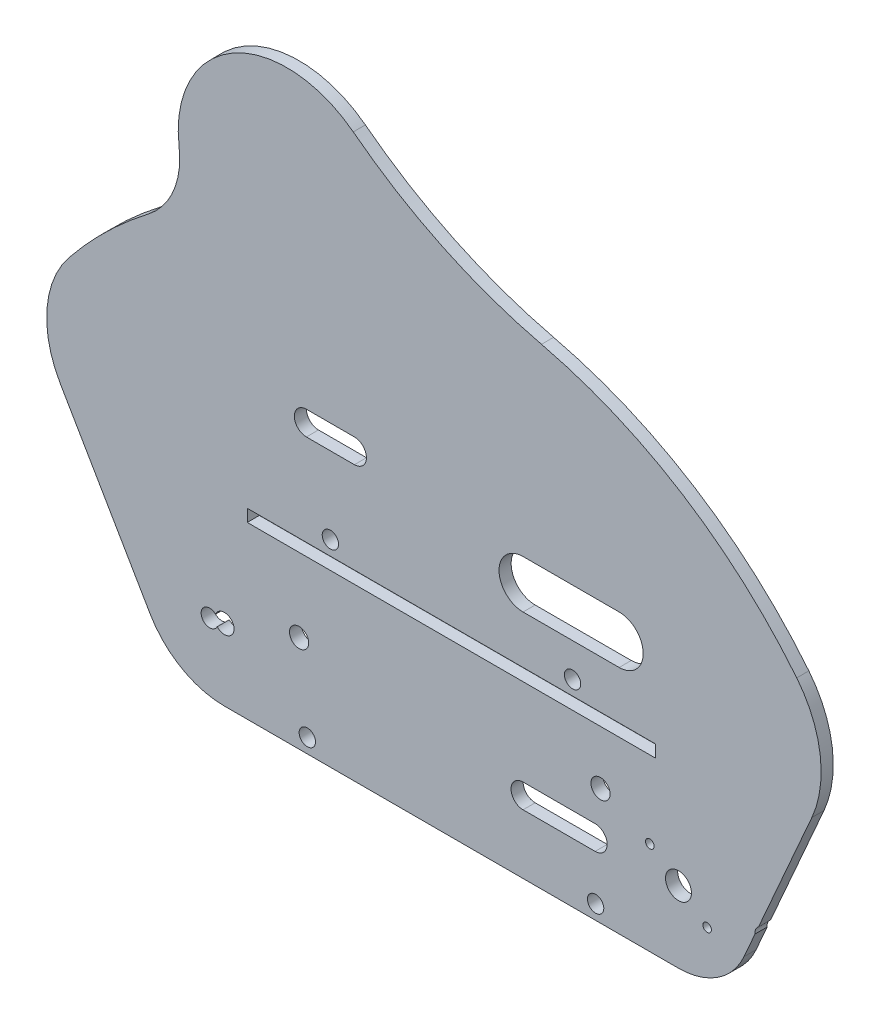
SolidWorks part; units mm, degrees
ref_plane "Front Plane" through (0, 0, 0) normal (0, 0, 1) x (1, 0, 0)
ref_plane "Top Plane" through (0, 0, 0) normal (0, 1, 0) x (1, 0, 0)
ref_plane "Right Plane" through (0, 0, 0) normal (1, 0, 0) x (0, 0, -1)
sketch "Sketch1" plane through (0, 0, 0) normal (0, 0, 1) x (1, 0, 0)
  line L8 (0, 18.9078) -> (120.015, 18.9078) construction
  line L18 (155.2575, 52.1157) -> (-50.9787, 52.1157) construction
  line L37 (0, 0) -> (120.015, 0)
  line L42 (19.7347, 25.5664) -> (0, 18.9078) construction
  line L55 (60.0075, 18.9078) -> (60.0075, 0) construction
  line L60 (137.3256, 11.3022) -> (120.015, 0) construction
  line L61 (-19.6481, 11.3022) -> (0, 0) construction
  line L62 (155.2575, 52.1157) -> (137.3256, 11.3022)
  line L63 (-43.3855, 52.1157) -> (-19.6481, 11.3022)
  line L64 (155.2575, 52.1157) -> (-43.3855, 52.1157) construction
  line L65 (137.3256, 11.3022) -> (-19.6481, 11.3022) construction
  line L66 (120.015, 18.9078) -> (99.4008, 30.8094) construction
  line L67 (151.2687, 82.096) -> (-41.1067, 82.096) construction
  circle A21 centre (120.015, 18.9078) radius 3.429
  circle A22 centre (0, 18.9078) radius 2.54
  arc A25 (137.3256, 11.3022) -> (120.015, 0) centre (120.015, 18.9078) cw
  circle A27 centre (19.7347, 25.5664) radius 2.54
  arc A34 (-19.6481, 11.3022) -> (0, 0) centre (0, 22.7296) ccw
  arc A36 (151.2687, 82.096) -> (155.2575, 52.1157) centre (128.6061, 63.8253) cw
  arc A37 (-41.1067, 82.096) -> (-43.3855, 52.1157) centre (-20.4591, 65.4498) ccw
  circle A38 centre (99.4008, 30.8094) radius 2.54
  arc A39 (151.2687, 82.096) -> (-41.1067, 82.096) centre (55.081, 4.5491) ccw
  dimension "D5" = 18.9078
  dimension "D8" = 59.818
  dimension "D3" = 20.6736
  dimension "D11" = 52.1157
  dimension "D13" = 30
  dimension "D2" = 6.858
  dimension "D10" = 5.08
  dimension "D15" = 123.554
  dimension "D4" = 18.645
  dimension "D6" = 20.8278
  dimension "D7" = 120.015
  dimension "D9" = 29.9803
  dimension "D12" = 52.1157
  dimension "D14" = 23.8032
extrude "Boss-Extrude1" add sketch "Sketch1" along normal blind 3.2004
sketch "Sketch2" plane through (0, 0, 0) normal (0, 0, -1) x (-1, 0, 0)
  line L0 (-60.0075, 52.1157) -> (-60.0075, 7.62) construction
  line L1 (-155.2575, 52.1157) -> (50.9787, 52.1157) construction
  line L14 (0, 18.9078) -> (-120.015, 18.9078) construction
  line L28 (-92.0115, 52.1157) -> (-76.0095, 52.1157) construction
  line L29 (-76.0095, 52.1157) -> (-44.0055, 52.1157) construction
  line L30 (-44.0055, 52.1157) -> (-28.0035, 52.1157) construction
  line L31 (-60.0075, 7.62) -> (-60.0075, 0) construction
  line L32 (-98.1075, 3.81) -> (-21.9075, 3.81) construction
  line L33 (0, 0) -> (-120.015, 0) construction
  circle A0 centre (-92.0115, 52.1157) radius 2.159
  circle A3 centre (-28.0035, 52.1157) radius 2.159
  circle A4 centre (-98.1075, 3.81) radius 2.159
  circle A6 centre (-21.9075, 3.81) radius 2.159
  point P11 (-36.0045, 52.1157)
  point P16 (-84.0105, 52.1157)
  point P21 (-60.0075, 3.81)
  dimension "D3" = 4.318
  dimension "D5" = 7.62
  dimension "D1" = 76.2
  dimension "D2" = 16.002
  dimension "D4" = 48.006
extrude "Cut-Extrude1" cut sketch "Sketch2" against normal blind 3.2004
sketch "Sketch10" plane through (0, 0, 0) normal (0, 0, -1) x (-1, 0, 0)
  line L0 (0, 0) -> (-120.015, 0) construction
  line L1 (-34.3535, 78.7857) -> (-21.6535, 78.7857)
  line L2 (-34.3535, 78.7857) -> (-34.3535, 72.4357) construction
  line L3 (-34.3535, 72.4357) -> (-21.6535, 72.4357)
  line L4 (-21.6535, 78.7857) -> (-21.6535, 72.4357) construction
  arc A0 (-21.6535, 78.7857) -> (-21.6535, 72.4357) centre (-21.6535, 75.6107) cw
  arc A1 (-34.3535, 78.7857) -> (-34.3535, 72.4357) centre (-34.3535, 75.6107) ccw
  circle A4 centre (-28.0035, 52.1157) radius 2.159 construction
  dimension "D3" = 20.32
  dimension "D4" = 6.35
  dimension "D1" = 12.7
  dimension "D2" = 6.35
extrude "Cut-Extrude8" cut sketch "Sketch10" against normal up to surface (3.2004 mm away) up to face at (19.7485, 3.81, 3.2004)
sketch "Sketch11" plane through (0, 0, 0) normal (0, 0, -1) x (-1, 0, 0)
  line L5 (-76.0095, 52.1157) -> (-44.0055, 52.1157) construction
  line L7 (-60.0075, 52.1157) -> (-60.0075, 48.3057) construction
  line L9 (-6.0325, 48.3057) -> (-113.9825, 48.3057)
  line L10 (-6.0325, 48.3057) -> (-6.0325, 45.0545)
  line L11 (-6.0325, 45.0545) -> (-113.9825, 45.0545)
  line L12 (-113.9825, 48.3057) -> (-113.9825, 45.0545)
  dimension "D1" = 107.95
  dimension "D2" = 3.81
  dimension "D5" = 3.2512
extrude "Cut-Extrude9" cut sketch "Sketch11" against normal up to surface (3.2004 mm away) up to face at (28.0035, 75.6107, 3.2004)
sketch "Sketch12" plane through (0, 0, 3.2004) normal (0, 0, 1) x (1, 0, 0)
  line L0 (112.4381, 24.6798) -> (127.5919, 13.1357) construction
  line L1 (78.9305, 73.7057) -> (104.3305, 73.7057)
  line L2 (0, 0) -> (120.015, 0) construction
  line L3 (78.9305, 73.7057) -> (78.9305, 61.0057) construction
  line L4 (78.9305, 61.0057) -> (104.3305, 61.0057)
  line L5 (104.3305, 73.7057) -> (104.3305, 61.0057) construction
  line L6 (78.9305, 22.0828) -> (97.9805, 22.0828)
  line L7 (78.9305, 22.0828) -> (78.9305, 15.7328) construction
  line L8 (78.9305, 15.7328) -> (97.9805, 15.7328)
  line L9 (97.9805, 22.0828) -> (97.9805, 15.7328) construction
  line L10 (97.9805, 18.9078) -> (120.015, 18.9078) construction
  line L11 (78.9305, 67.3557) -> (104.3305, 67.3557) construction
  line L12 (91.6305, 67.3557) -> (91.6305, 52.1157) construction
  line L13 (92.0115, 52.1157) -> (76.0095, 52.1157) construction
  circle A0 centre (112.4381, 24.6798) radius 1.1303
  circle A1 centre (127.5919, 13.1357) radius 1.1303
  arc A4 (104.3305, 73.7057) -> (104.3305, 61.0057) centre (104.3305, 67.3557) cw
  arc A5 (78.9305, 73.7057) -> (78.9305, 61.0057) centre (78.9305, 67.3557) ccw
  circle A6 centre (120.015, 18.9078) radius 3.429 construction
  arc A7 (97.9805, 22.0828) -> (97.9805, 15.7328) centre (97.9805, 18.9078) cw
  arc A8 (78.9305, 22.0828) -> (78.9305, 15.7328) centre (78.9305, 18.9078) ccw
  point P10 (120.015, 18.9078)
  dimension "D1" = 2.2606
  dimension "D4" = 7.62
  dimension "D2" = 37.3
  dimension "D3" = 19.05
  dimension "D5" = 12.7
  dimension "D6" = 6.35
  dimension "D7" = 19.05
  dimension "D8" = 38.923
  dimension "D9" = 25.4
extrude "Cut-Extrude11" cut sketch "Sketch12" against normal up to surface (3.2004 mm away) up to face at (60.0075, 46.6801, 0)
sketch "Sketch13" plane through (0, 0, 3.2004) normal (0, 0, 1) x (1, 0, 0)
  circle A0 centre (-3.9143, 18.2241) radius 2.2479
  circle A1 centre (142.479, 18.2241) radius 2.2479
  circle A2 centre (142.479, 18.2241) radius 1.651 construction
  circle A3 centre (-3.9143, 18.2241) radius 1.651 construction
  dimension "D1" = 4.4958
extrude "Cut-Extrude12" cut sketch "Sketch13" against normal up to surface (3.2004 mm away) up to face at (91.6305, 67.3557, 0)
sketch "Sketch15" plane through (0, 0, 0) normal (0, 0, -1) x (-1, 0, 0)
  line L0 (-83.8046, 124.7179) -> (-34.0526, 148.4576) construction
  line L1 (-83.8046, 124.7179) -> (20.1056, 102.5928)
  line L2 (-83.8046, 124.7179) -> (-55.081, 82.096) construction
  line L3 (-151.2687, 82.096) -> (41.1067, 82.096) construction
  arc A0 (-83.8046, 124.7179) -> (-34.0526, 148.4576) centre (-114.4589, 252.964) ccw
  arc A2 (-34.0526, 148.4576) -> (11.9851, 122.0607) centre (-16.5269, 125.6789) cw
  arc A3 (11.9851, 122.0607) -> (20.1056, 102.5928) centre (32.9907, 119.395) ccw
  arc A4 (41.1067, 82.096) -> (-151.2687, 82.096) centre (-55.081, 4.5491) ccw construction
  dimension "D1" = 55.1256
  dimension "D2" = 56.023
  dimension "D3" = 106.2396
  dimension "D4" = 37.529
extrude "Boss-Extrude2" add sketch "Sketch15" against normal up to surface (3.2004 mm away) up to face at (-1.8133, 18.591, 3.2004)
